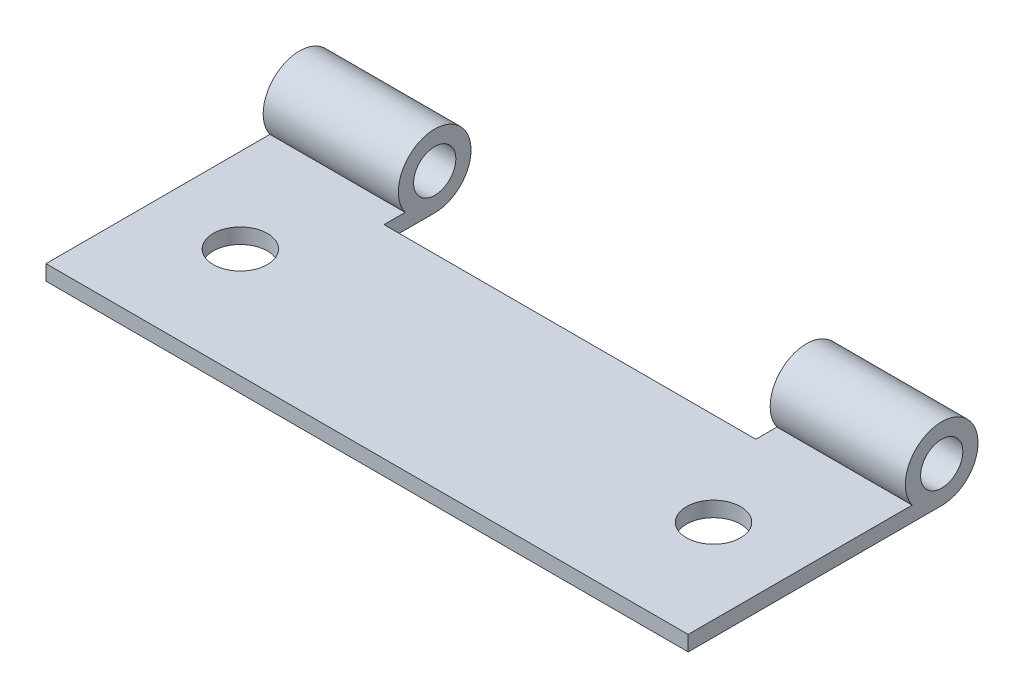
SolidWorks part; units mm, degrees
ref_plane "前视基准面" through (0, 0, 0) normal (0, 0, 1) x (1, 0, 0)
ref_plane "上视基准面" through (0, 0, 0) normal (0, 1, 0) x (1, 0, 0)
ref_plane "右视基准面" through (0, 0, 0) normal (1, 0, 0) x (0, 0, -1)
sketch "草图1" plane through (0, 0, 0) normal (1, 0, 0) x (0, 0, -1)
  line L0 (0, -2.15) -> (-15, -2.15)
  line L1 (-15, -2.15) -> (-15, -1.25)
  line L2 (-1.7493, -1.25) -> (-15, -1.25)
  circle A0 centre (0, 0) radius 1.25
  arc A1 (0, -2.15) -> (-1.7493, -1.25) centre (0, 0) ccw
  dimension "D1" = 4.3
  dimension "D2" = 0.9
  dimension "D3" = 15
extrude "凸台-拉伸1" add sketch "草图1" along normal blind 38
sketch "草图2" plane through (0, 0, 0) normal (0, 1, 0) x (1, 0, 0)
  line L0 (19, 6.6145) -> (19, -19.2902) construction
  line L1 (0, -1.7493) -> (0, -15) construction
  line L2 (38, -1.7493) -> (38, -15) construction
  line L3 (0, 2.15) -> (0, -2.15) construction
  line L4 (8, 4.8901) -> (30, 4.8901)
  line L5 (8, 4.8901) -> (8, -3)
  line L6 (8, -3) -> (30, -3)
  line L7 (30, 4.8901) -> (30, -3)
  line L8 (38, -15) -> (0, -15) construction
  circle A0 centre (33, -8.5) radius 1.6
  circle A1 centre (5, -8.5) radius 1.6
  dimension "D3" = 8.5
  dimension "D4" = 3.2
  dimension "D5" = 28
  dimension "D1" = 8
  dimension "D2" = 12
extrude "切除-拉伸1" cut sketch "草图2" against normal mid plane 38
